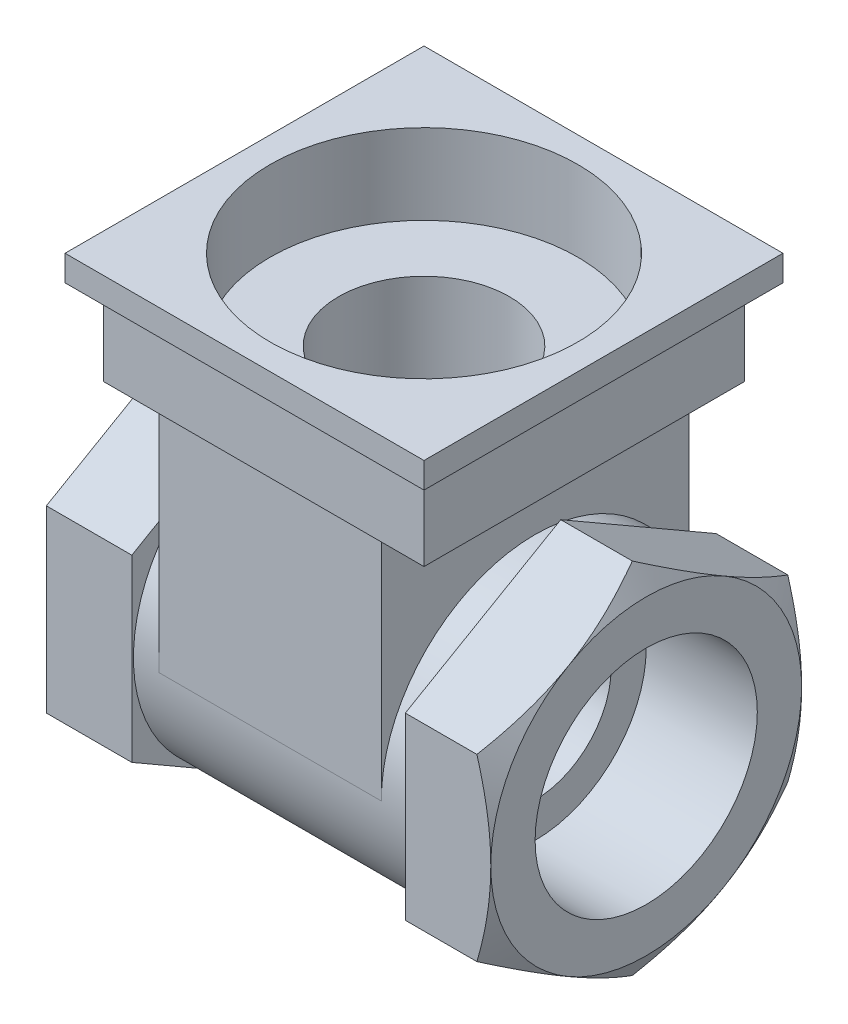
SolidWorks part; units mm, degrees
ref_plane "Front Plane" through (0, 0, 0) normal (0, 0, 1) x (1, 0, 0)
ref_plane "Top Plane" through (0, 0, 0) normal (0, 1, 0) x (1, 0, 0)
ref_plane "Right Plane" through (0, 0, 0) normal (1, 0, 0) x (0, 0, -1)
sketch "Sketch1" plane through (0, 0, 0) normal (1, 0, 0) x (0, 0, -1)
  circle A0 centre (0, 0) radius 18
  dimension "D1" = 36
extrude "Boss-Extrude1" add sketch "Sketch1" along normal mid plane 32
sketch "Sketch2" plane through (16, 0, 0) normal (1, 0, 0) x (0, 0, -1)
  line L1 (0, 21) -> (-18.1865, 10.5)
  line L2 (-18.1865, 10.5) -> (-18.1865, -10.5)
  line L3 (-18.1865, -10.5) -> (0, -21)
  line L4 (0, -21) -> (18.1865, -10.5)
  line L5 (18.1865, -10.5) -> (18.1865, 10.5)
  line L6 (18.1865, 10.5) -> (0, 21)
  circle A0 centre (0, 0) radius 18.1865 construction
  point P1 (0, 0)
  dimension "D1" = 42
extrude "Boss-Extrude2" add sketch "Sketch2" along normal blind 10
sketch "Sketch4" plane through (-16, 0, 0) normal (-1, 0, 0) x (0, 0, 1)
  line L6 (18.1865, 10.5) -> (0, 21)
  line L7 (18.1865, -10.5) -> (18.1865, 10.5)
  line L8 (0, -21) -> (18.1865, -10.5)
  line L9 (-18.1865, -10.5) -> (0, -21)
  line L10 (-18.1865, 10.5) -> (-18.1865, -10.5)
  line L11 (0, 21) -> (-18.1865, 10.5)
  line L12 (18.1865, 10.5) -> (0, 21)
  line L13 (18.1865, -10.5) -> (18.1865, 10.5)
  line L14 (0, -21) -> (18.1865, -10.5)
  line L15 (-18.1865, -10.5) -> (0, -21)
  line L16 (-18.1865, 10.5) -> (-18.1865, -10.5)
  line L17 (0, 21) -> (-18.1865, 10.5)
  circle A1 centre (0, 0) radius 18
  circle A2 centre (0, 0) radius 18
  dimension "D1" = 0
  dimension "D2" = 0
extrude "Boss-Extrude6" add sketch "Sketch4" along normal blind 10 contours L12 L17 L16 L15 L14 L13
sketch "Sketch5" plane through (-26, 0, 0) normal (-1, 0, 0) x (0, 0, 1)
  circle A0 centre (0, 0) radius 13
  dimension "D1" = 26
extrude "Cut-Extrude1" cut sketch "Sketch5" against normal blind 13
sketch "Sketch6" plane through (26, 0, 0) normal (1, 0, 0) x (0, 0, -1)
  circle A0 centre (0, 0) radius 13
  dimension "D1" = 26
extrude "Cut-Extrude2" cut sketch "Sketch6" against normal blind 13
sketch "Sketch7" plane through (13, 0, 0) normal (1, 0, 0) x (0, 0, -1)
  circle A0 centre (0, 0) radius 8.9
  dimension "D1" = 17.8
extrude "Cut-Extrude3" cut sketch "Sketch7" against normal through all
sketch "Sketch8" plane through (26, 0, 0) normal (1, 0, 0) x (0, 0, -1)
  circle A0 centre (0, 0) radius 18.1865
extrude "Cut-Extrude4" cut sketch "Sketch8" against normal blind 5 draft 60 flip side to cut
sketch "Sketch9" plane through (-26, 0, 0) normal (-1, 0, 0) x (0, 0, 1)
  circle A0 centre (0, 0) radius 18.1865
extrude "Cut-Extrude5" cut sketch "Sketch9" against normal blind 5 draft 60
ref_plane "Plane1" through (0, 40, 0) normal (0, 1, 0) x (1, 0, 0)
sketch "Sketch10" plane through (0, 40, 0) normal (0, 1, 0) x (1, 0, 0)
  line L1 (-21, -21) -> (21, -21)
  line L2 (-21, -21) -> (-21, 21)
  line L3 (-21, 21) -> (21, 21)
  line L4 (21, -21) -> (21, 21)
  line L5 (-21, -21) -> (21, 21) construction
  line L6 (-21, 21) -> (21, -21) construction
  point P0 (0, 0)
  dimension "D1" = 42
  dimension "D2" = 42
extrude "Boss-Extrude8" add sketch "Sketch10" against normal blind 3 separate body
sketch "Sketch11" plane through (0, 40, 0) normal (0, 1, 0) x (1, 0, 0)
  line L1 (-18.75, -18.75) -> (18.75, -18.75)
  line L2 (-18.75, -18.75) -> (-18.75, 18.75)
  line L3 (-18.75, 18.75) -> (18.75, 18.75)
  line L4 (18.75, -18.75) -> (18.75, 18.75)
  line L5 (-18.75, -18.75) -> (18.75, 18.75) construction
  line L6 (-18.75, 18.75) -> (18.75, -18.75) construction
  point P1 (0, 0)
  dimension "D1" = 37.5
  dimension "D2" = 37.5
extrude "Boss-Extrude9" add sketch "Sketch11" against normal blind 13
sketch "Sketch12" plane through (0, 40, 0) normal (0, 1, 0) x (1, 0, 0)
  line L1 (-13, -18) -> (13, -18)
  line L2 (-13, -18) -> (-13, 18)
  line L3 (-13, 18) -> (13, 18)
  line L4 (13, -18) -> (13, 18)
  line L5 (-13, -18) -> (13, 18) construction
  line L6 (-13, 18) -> (13, -18) construction
  point P0 (0, 0)
  dimension "D1" = 36
  dimension "D2" = 26
extrude "Boss-Extrude10" add sketch "Sketch12" against normal up to body
sketch "Sketch13" plane through (0, 0, 0) normal (0, 0, 1) x (1, 0, 0)
  line L0 (0, 40) -> (0, -9.9)
  line L1 (23.1, 40) -> (-23.1, 40) construction
  line L2 (0, -9.9) -> (7, -9.9)
  line L3 (7, -9.9) -> (9, 16.1)
  line L4 (9, 16.1) -> (10, 16.1)
  line L5 (10, 16.1) -> (10, 30.6043)
  line L6 (10, 30.6043) -> (18, 30.6043)
  line L7 (18, 30.6043) -> (18, 40)
  line L8 (18, 40) -> (0, 40)
  line L9 (-13, -8.9) -> (13, -8.9) construction
  dimension "D1" = 7
  dimension "D2" = 1
  dimension "D3" = 26
  dimension "D4" = 9
  dimension "D5" = 10
  dimension "D6" = 18
revolve "Cut-Revolve1" cut sketch "Sketch13" angle 360 about L0
